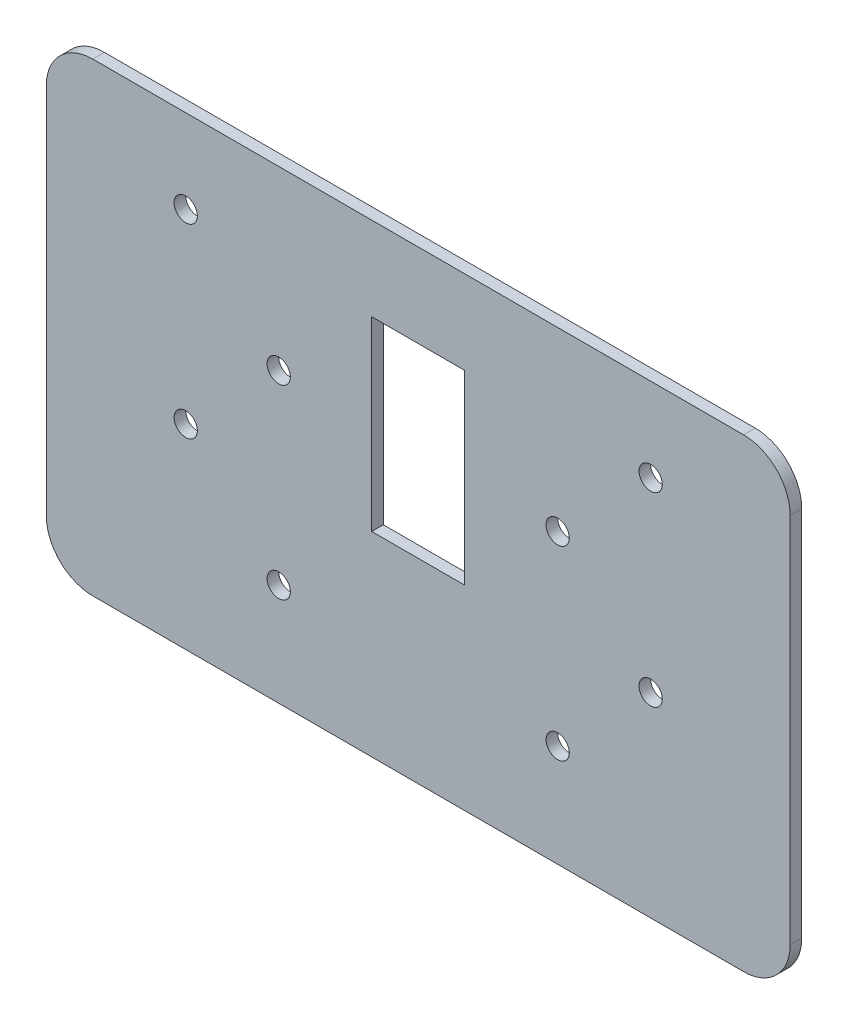
SolidWorks part; units mm, degrees
ref_plane "Front Plane" through (0, 0, 0) normal (0, 0, 1) x (1, 0, 0)
ref_plane "Top Plane" through (0, 0, 0) normal (0, 1, 0) x (1, 0, 0)
ref_plane "Right Plane" through (0, 0, 0) normal (1, 0, 0) x (0, 0, -1)
sketch "Sketch1" plane through (0, 0, 0) normal (0, 0, 1) x (1, 0, 0)
  line L0 (290.4194, 380.9708) -> (315.8194, 380.9708) construction
  line L1 (214.2194, 454.6308) -> (392.0194, 454.6308)
  line L2 (201.5194, 441.9308) -> (201.5194, 340.3308)
  line L3 (214.2194, 327.6308) -> (392.0194, 327.6308)
  line L4 (404.7194, 441.9308) -> (404.7194, 340.3308)
  line L5 (315.8194, 380.9708) -> (315.8194, 431.7708) construction
  line L6 (315.8194, 431.7708) -> (290.4194, 431.7708) construction
  line L7 (290.4194, 431.7708) -> (290.4194, 380.9708) construction
  line L8 (290.4194, 380.9708) -> (315.8194, 380.9708)
  line L9 (315.8194, 380.9708) -> (315.8194, 431.7708)
  line L10 (315.8194, 431.7708) -> (290.4194, 431.7708)
  line L11 (290.4194, 431.7708) -> (290.4194, 380.9708)
  line L12 (303.1194, 454.6308) -> (303.1194, 327.6308) construction
  line L47 (248.8374, 457.9915) -> (248.9748, 468.1468)
  line L48 (248.9748, 468.1468) -> (172.713, 469.1781)
  line L49 (172.713, 469.1781) -> (172.713, 459.0181)
  line L50 (172.713, 459.0181) -> (96.52, 460.0485)
  line L51 (96.52, 460.0485) -> (96.52, 470.2085)
  line L52 (96.52, 470.2085) -> (20.32, 471.239)
  line L53 (20.32, 471.239) -> (20.32, 455.9603)
  line L54 (20.32, 455.9603) -> (0, 455.9603)
  line L55 (0, 455.9603) -> (0, 392.2753)
  line L56 (0, 392.2753) -> (20.32, 392.2753)
  line L57 (20.32, 392.2753) -> (20.32, 328.5902)
  line L58 (20.32, 328.5902) -> (0, 328.5902)
  line L59 (0, 328.5902) -> (0, 264.9051)
  line L60 (0, 264.9051) -> (20.32, 264.9051)
  line L61 (20.32, 264.9051) -> (20.32, 201.2201)
  line L62 (20.32, 201.2201) -> (0, 201.2201)
  line L63 (0, 201.2201) -> (0, 137.535)
  line L64 (0, 137.535) -> (20.32, 137.535)
  line L65 (20.32, 137.535) -> (20.32, 73.85)
  line L66 (20.32, 73.85) -> (0, 73.85)
  line L67 (0, 73.85) -> (0, 10.1649)
  line L68 (0, 10.1649) -> (20.32, 10.1649)
  line L69 (20.32, 10.1649) -> (115.0678, 14.0912)
  line L70 (115.0678, 14.0912) -> (115.4883, 3.9437)
  line L71 (115.4883, 3.9437) -> (210.6566, 7.8874)
  line L72 (210.6566, 7.8874) -> (210.2361, 18.0349)
  line L73 (210.2361, 18.0349) -> (305.4045, 21.9786)
  line L74 (305.4045, 21.9786) -> (305.825, 11.8311)
  line L75 (305.825, 11.8311) -> (400.9933, 15.7748)
  line L76 (400.9933, 15.7748) -> (400.5728, 25.9223)
  line L77 (400.5728, 25.9223) -> (495.7411, 29.866)
  line L78 (495.7411, 29.866) -> (496.1616, 19.7186)
  line L79 (496.1616, 19.7186) -> (591.3299, 23.6623)
  line L80 (591.3299, 23.6623) -> (590.9094, 33.8097)
  line L81 (590.9094, 33.8097) -> (676.3383, 37.3499)
  line L82 (676.3383, 37.3499) -> (676.3383, 122.6762)
  line L83 (676.3383, 122.6762) -> (686.4983, 122.6762)
  line L84 (686.4983, 122.6762) -> (686.4983, 207.5989)
  line L85 (686.4983, 207.5989) -> (676.3383, 207.5989)
  line L86 (676.3383, 207.5989) -> (676.3383, 292.5217)
  line L87 (676.3383, 292.5217) -> (686.4983, 292.5217)
  line L88 (686.4983, 292.5217) -> (686.4983, 377.4444)
  line L89 (686.4983, 377.4444) -> (676.3383, 377.4444)
  line L90 (676.3383, 377.4444) -> (676.3383, 462.3671)
  line L91 (676.3383, 462.3671) -> (325.1678, 467.1163)
  line L92 (325.1678, 467.1163) -> (325.0304, 456.9611)
  line L93 (325.0304, 456.9611) -> (248.8374, 457.9915)
  line L94 (248.8374, 457.9915) -> (248.9748, 468.1468)
  line L95 (248.9748, 468.1468) -> (172.713, 469.1781)
  line L96 (172.713, 469.1781) -> (172.713, 459.0181)
  line L97 (172.713, 459.0181) -> (96.52, 460.0485)
  line L98 (96.52, 460.0485) -> (96.52, 470.2085)
  line L99 (96.52, 470.2085) -> (20.32, 471.239)
  line L100 (20.32, 471.239) -> (20.32, 455.9603)
  line L101 (20.32, 455.9603) -> (0, 455.9603)
  line L102 (0, 455.9603) -> (0, 392.2753)
  line L103 (0, 392.2753) -> (20.32, 392.2753)
  line L104 (20.32, 392.2753) -> (20.32, 328.5902)
  line L105 (20.32, 328.5902) -> (0, 328.5902)
  line L106 (0, 328.5902) -> (0, 264.9051)
  line L107 (0, 264.9051) -> (20.32, 264.9051)
  line L108 (20.32, 264.9051) -> (20.32, 201.2201)
  line L109 (20.32, 201.2201) -> (0, 201.2201)
  line L110 (0, 201.2201) -> (0, 137.535)
  line L111 (0, 137.535) -> (20.32, 137.535)
  line L112 (20.32, 137.535) -> (20.32, 73.85)
  line L113 (20.32, 73.85) -> (0, 73.85)
  line L114 (0, 73.85) -> (0, 10.1649)
  line L115 (0, 10.1649) -> (20.32, 10.1649)
  line L116 (20.32, 10.1649) -> (115.0678, 14.0912)
  line L117 (115.0678, 14.0912) -> (115.4883, 3.9437)
  line L118 (115.4883, 3.9437) -> (210.6566, 7.8874)
  line L119 (210.6566, 7.8874) -> (210.2361, 18.0349)
  line L120 (210.2361, 18.0349) -> (305.4045, 21.9786)
  line L121 (305.4045, 21.9786) -> (305.825, 11.8311)
  line L122 (305.825, 11.8311) -> (400.9933, 15.7748)
  line L123 (400.9933, 15.7748) -> (400.5728, 25.9223)
  line L124 (400.5728, 25.9223) -> (495.7411, 29.866)
  line L125 (495.7411, 29.866) -> (496.1616, 19.7186)
  line L126 (496.1616, 19.7186) -> (591.3299, 23.6623)
  line L127 (591.3299, 23.6623) -> (590.9094, 33.8097)
  line L128 (590.9094, 33.8097) -> (676.3383, 37.3499)
  line L129 (676.3383, 37.3499) -> (676.3383, 122.6762)
  line L130 (676.3383, 122.6762) -> (686.4983, 122.6762)
  line L131 (686.4983, 122.6762) -> (686.4983, 207.5989)
  line L132 (686.4983, 207.5989) -> (676.3383, 207.5989)
  line L133 (676.3383, 207.5989) -> (676.3383, 292.5217)
  line L134 (676.3383, 292.5217) -> (686.4983, 292.5217)
  line L135 (686.4983, 292.5217) -> (686.4983, 377.4444)
  line L136 (686.4983, 377.4444) -> (676.3383, 377.4444)
  line L137 (676.3383, 377.4444) -> (676.3383, 462.3671)
  line L138 (676.3383, 462.3671) -> (325.1678, 467.1163)
  line L139 (325.1678, 467.1163) -> (325.0304, 456.9611)
  line L140 (325.0304, 456.9611) -> (248.8374, 457.9915)
  circle A0 centre (265.0194, 406.3708) radius 3.175 construction
  circle A1 centre (265.0194, 406.3708) radius 3.175
  circle A2 centre (239.6194, 431.7708) radius 3.175 construction
  circle A3 centre (239.6194, 431.7708) radius 3.175
  circle A4 centre (239.6194, 380.9708) radius 3.175 construction
  circle A5 centre (239.6194, 380.9708) radius 3.175
  circle A6 centre (366.6194, 380.9708) radius 3.175 construction
  circle A7 centre (366.6194, 380.9708) radius 3.175
  circle A8 centre (341.2194, 406.3708) radius 3.175 construction
  circle A9 centre (341.2194, 406.3708) radius 3.175
  circle A10 centre (366.6194, 431.7708) radius 3.175 construction
  circle A11 centre (366.6194, 431.7708) radius 3.175
  arc A12 (214.2194, 454.6308) -> (201.5194, 441.9308) centre (214.2194, 441.9308) ccw
  arc A13 (392.0194, 327.6308) -> (404.7194, 340.3308) centre (392.0194, 340.3308) ccw
  arc A14 (201.5194, 340.3308) -> (214.2194, 327.6308) centre (214.2194, 340.3308) ccw
  arc A15 (392.0194, 454.6308) -> (404.7194, 441.9308) centre (392.0194, 441.9308) cw
  circle A16 centre (265.0194, 355.5708) radius 3.175 construction
  circle A17 centre (341.2194, 355.5708) radius 3.175 construction
  circle A18 centre (265.0194, 355.5708) radius 3.175
  circle A19 centre (341.2194, 355.5708) radius 3.175
  point P58 (303.1194, 431.7708)
  point P64 (201.5194, 454.6308)
  point P74 (201.5194, 327.6308)
  point P80 (404.7194, 454.6308)
  dimension "D5" = 12.7
  dimension "D2" = 127
  dimension "D3" = 203.2
  dimension "D4" = 22.86
  dimension "D1" = 0
extrude "Boss-Extrude1" add sketch "Sketch1" along normal blind 3.175 contours L1 L12 L10 L9 L8 L3 L4 A7 A9 A11 | L12 L1 L2 L3 L8 L11 L10 A5 A3 A1
